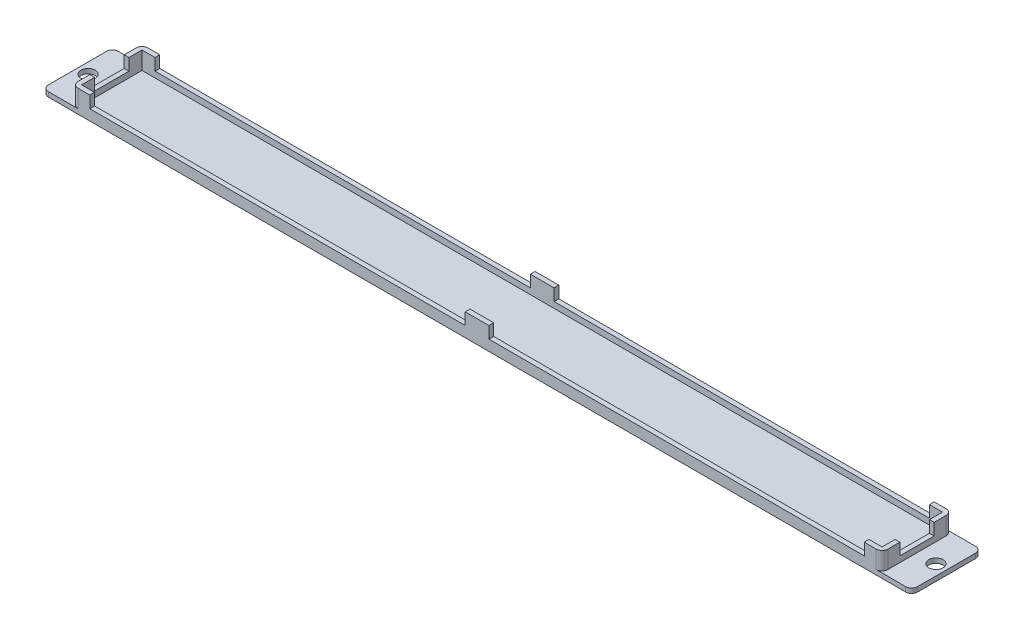
SolidWorks part; units mm, degrees
ref_plane "Plan de face" through (0, 0, 0) normal (0, 0, 1) x (1, 0, 0)
ref_plane "Plan de dessus" through (0, 0, 0) normal (0, 1, 0) x (1, 0, 0)
ref_plane "Plan de droite" through (0, 0, 0) normal (1, 0, 0) x (0, 0, -1)
sketch "Esquisse1" plane through (0, 0, 0) normal (0, 1, 0) x (1, 0, 0)
  line L1 (0, 0) -> (136.8, 0)
  line L2 (0, 0) -> (0, 11.8)
  line L3 (0, 11.8) -> (136.8, 11.8)
  line L4 (136.8, 0) -> (136.8, 11.8)
  dimension "D1" = 11.8
  dimension "D2" = 136.8
extrude "Boss.-Extru.1" add sketch "Esquisse1" along normal blind 0.8
sketch "Esquisse2" plane through (0, 0.8, 0) normal (0, 1, 0) x (1, 0, 0)
  line L0 (0.8, 11) -> (0.8, 0.8)
  line L1 (0, 11.8) -> (136.8, 11.8)
  line L2 (0, 11.8) -> (0, 0)
  line L3 (0, 0) -> (136.8, 0)
  line L4 (136.8, 11.8) -> (136.8, 0)
  line L5 (0.8, 0.8) -> (136, 0.8)
  line L6 (136, 11) -> (136, 0.8)
  line L7 (0.8, 11) -> (136, 11)
  dimension "D1" = 0.8
extrude "Boss.-Extru.2" add sketch "Esquisse2" along normal blind 1
sketch "Esquisse3" plane through (0, 1.8, 0) normal (0, 1, 0) x (1, 0, 0)
  line L0 (0, 5.9) -> (136.8, 5.9) construction
  line L1 (0, 11.8) -> (0, 0) construction
  line L2 (136.8, 0) -> (136.8, 11.8) construction
  line L3 (0, 3) -> (0.8, 3)
  line L4 (0.8, 11) -> (0.8, 0.8) construction
  line L5 (0.8, 3) -> (0.8, 0.8)
  line L6 (0.8, 0.8) -> (3, 0.8)
  line L7 (0.8, 0.8) -> (136, 0.8) construction
  line L8 (3, 0.8) -> (3, 0)
  line L9 (0, 0) -> (136.8, 0) construction
  line L10 (3, 0) -> (0, 0)
  line L11 (0, 0) -> (0, 3)
  line L12 (0, 11.8) -> (0, 8.8)
  line L13 (3, 11.8) -> (0, 11.8)
  line L14 (3, 11) -> (3, 11.8)
  line L15 (0.8, 11) -> (3, 11)
  line L16 (0.8, 8.8) -> (0.8, 11)
  line L17 (0, 8.8) -> (0.8, 8.8)
  line L18 (136.8, 11.8) -> (0, 11.8) construction
  line L19 (136, 11) -> (133.8, 11)
  line L23 (136, 11) -> (0.8, 11) construction
  line L24 (66.4, 11.8) -> (70.4, 11.8)
  line L25 (66.4, 11.8) -> (66.4, 11)
  line L26 (66.4, 11) -> (70.4, 11)
  line L27 (70.4, 11.8) -> (70.4, 11)
  line L28 (0, 11.8) -> (136.8, 11.8) construction
  line L33 (70.4, 0) -> (70.4, 0.8)
  line L34 (66.4, 0.8) -> (70.4, 0.8)
  line L35 (66.4, 0) -> (66.4, 0.8)
  line L36 (66.4, 0) -> (70.4, 0)
  line L37 (68.4, 11.8) -> (68.4, 0) construction
  line L38 (136.8, 8.8) -> (136, 8.8)
  line L39 (136, 8.8) -> (136, 11)
  line L40 (136, 11) -> (133.8, 11)
  line L41 (133.8, 11) -> (133.8, 11.8)
  line L42 (133.8, 11.8) -> (136.8, 11.8)
  line L43 (136.8, 11.8) -> (136.8, 8.8)
  line L44 (136.8, 0) -> (136.8, 3)
  line L45 (133.8, 0) -> (136.8, 0)
  line L46 (133.8, 0.8) -> (133.8, 0)
  line L47 (136, 0.8) -> (133.8, 0.8)
  line L48 (136, 3) -> (136, 0.8)
  line L49 (136.8, 3) -> (136, 3)
  point P39 (68.4, 11.8)
  point P42 (68.4, 11.8)
  dimension "D1" = 3
  dimension "D3" = 4
extrude "Boss.-Extru.3" add sketch "Esquisse3" along normal blind 2
sketch "Esquisse4" plane through (136.8, 0, 0) normal (1, 0, 0) x (0, 0, -1)
  line L1 (11.8, 0) -> (0, 0)
  line L2 (11.8, 0) -> (11.8, 0.8)
  line L3 (11.8, 0.8) -> (0, 0.8)
  line L4 (0, 0) -> (0, 0.8)
  line L5 (0, 3.8) -> (0, 0) construction
  dimension "D1" = 0.8
extrude "Boss.-Extru.4" add sketch "Esquisse4" along normal blind 5
sketch "Esquisse5" plane through (0, 0, 0) normal (-1, 0, 0) x (0, 0, 1)
  line L1 (-11.8, 0) -> (0, 0)
  line L2 (-11.8, 0) -> (-11.8, 0.8)
  line L3 (-11.8, 0.8) -> (0, 0.8)
  line L4 (0, 0) -> (0, 0.8)
  line L5 (0, 3.8) -> (0, 0) construction
  dimension "D1" = 0.8
extrude "Boss.-Extru.5" add sketch "Esquisse5" along normal blind 5
sketch "Esquisse6" plane through (0, 0, 0) normal (0, -1, 0) x (1, 0, 0)
  line L1 (68.4, -11.8) -> (68.4, 0) construction
  line L2 (141.8, -11.8) -> (-5, -11.8) construction
  line L3 (-5, 0) -> (141.8, 0) construction
  line L4 (141.8, -11.8) -> (141.8, 0) construction
  line L6 (136.8, -11.8) -> (136.8, 0) construction
  circle A0 centre (140, -5.9) radius 1.2
  circle A1 centre (-3.2, -5.9) radius 1.2
  point P4 (141.8, -5.9)
  dimension "D1" = 2.4
  dimension "D2" = 3.2
extrude "Enlèv. mat.-Extru.1" cut sketch "Esquisse6" against normal blind 4
fillet "Congé1" radius 1 8 edges at (-5, 0.4, 0) (-5, 0.4, -11.8) (0, 2.3, -11.8) (0, 2.3, 0) (136.8, 2.3, -11.8) (136.8, 2.3, 0) (141.8, 0.4, 0) (141.8, 0.4, -11.8)
